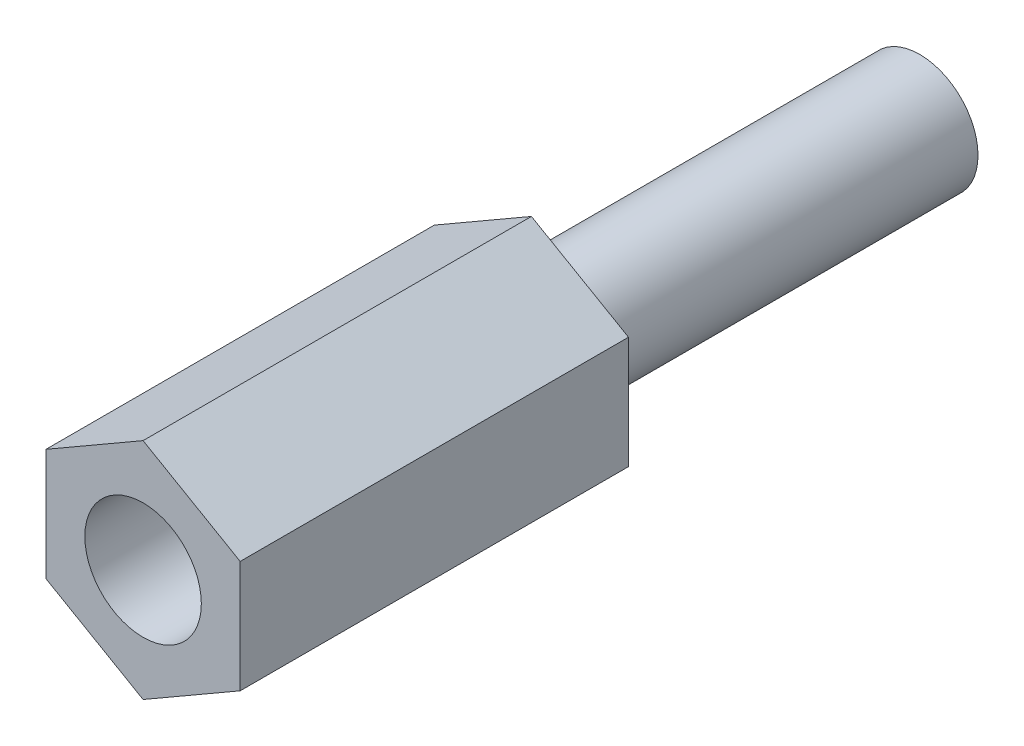
SolidWorks part; units mm, degrees
ref_plane "Plan de face" through (0, 0, 0) normal (0, 0, 1) x (1, 0, 0)
ref_plane "Plan de dessus" through (0, 0, 0) normal (0, 1, 0) x (1, 0, 0)
ref_plane "Plan de droite" through (0, 0, 0) normal (1, 0, 0) x (0, 0, -1)
sketch "Esquisse1" plane through (0, 0, 0) normal (0, 0, 1) x (1, 0, 0)
  line L1 (0, -2.8868) -> (2.5, -1.4434)
  line L2 (2.5, -1.4434) -> (2.5, 1.4434)
  line L3 (2.5, 1.4434) -> (0, 2.8868)
  line L4 (0, 2.8868) -> (-2.5, 1.4434)
  line L5 (-2.5, 1.4434) -> (-2.5, -1.4434)
  line L6 (-2.5, -1.4434) -> (0, -2.8868)
  circle A0 centre (0, 0) radius 2.5 construction
  circle A1 centre (0, 0) radius 1.5
  dimension "D1" = 3
  dimension "D2" = 5
extrude "Boss.-Extru.2" add sketch "Esquisse1" along normal blind 10 contours A1 | L1 L2 L3 L4 L5 L6
sketch "Esquisse3" plane through (0, 0, 0) normal (0, 0, -1) x (-1, 0, 0)
  circle A0 centre (0, 0) radius 1.5
extrude "Boss.-Extru.3" add sketch "Esquisse3" against normal blind 2 and the other way blind 10
